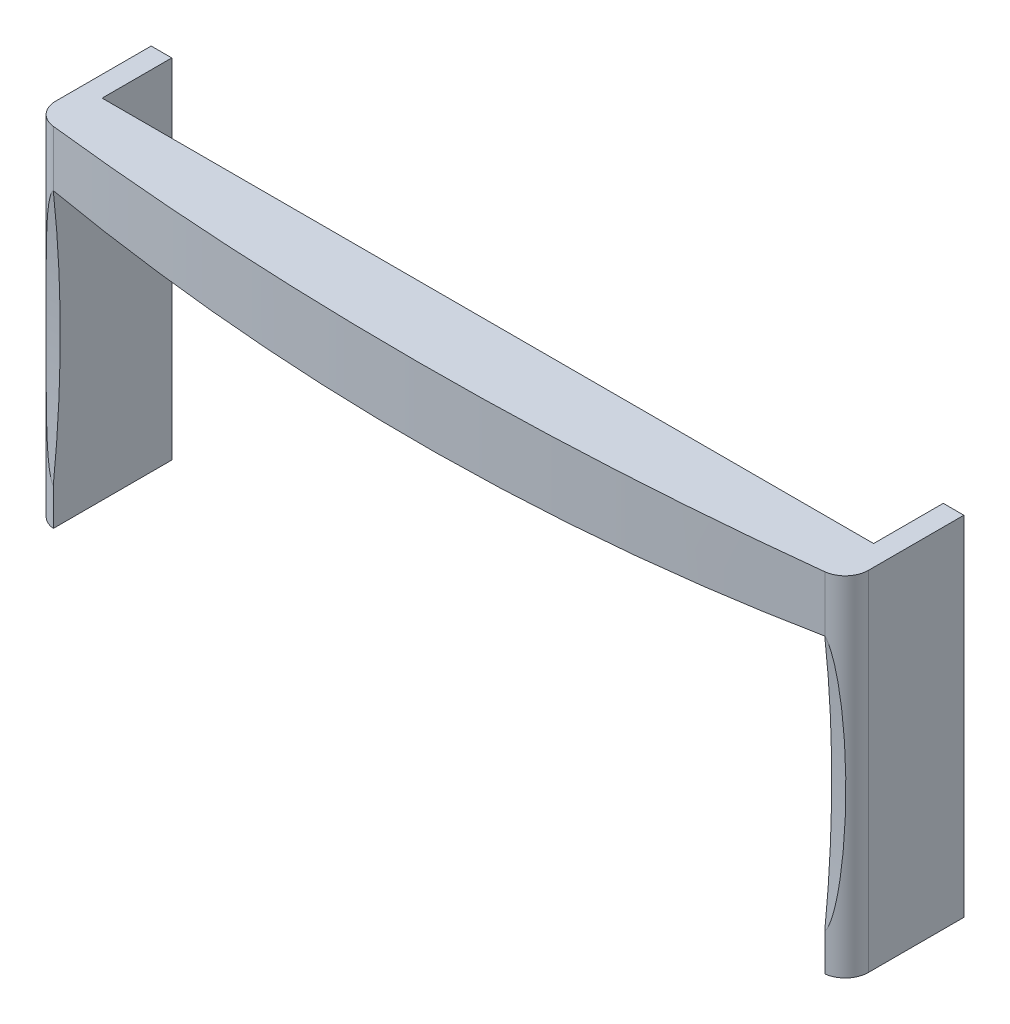
SolidWorks part; units mm, degrees
ref_plane "Front Plane" through (0, 0, 0) normal (0, 0, 1) x (1, 0, 0)
ref_plane "Top Plane" through (0, 0, 0) normal (0, 1, 0) x (1, 0, 0)
ref_plane "Right Plane" through (0, 0, 0) normal (1, 0, 0) x (0, 0, -1)
sketch "Sketch1" plane through (0, 0, 0) normal (0, 1, 0) x (1, 0, 0)
  line L0 (-87.5, 2.5) -> (-87.5, 12.5)
  line L5 (-87.5, 2.5) -> (87.5, -2.5) construction
  line L6 (-87.5, -2.5) -> (87.5, 2.5) construction
  line L7 (-87.5, 12.5) -> (87.5, 12.5)
  line L8 (87.5, 12.5) -> (87.5, 2.5)
  line L9 (-87.5, 2.5) -> (87.5, 2.5) construction
  arc A0 (-87.5, 2.5) -> (87.5, 2.5) centre (0, 735.8592) ccw
  point P0 (0, 0)
  point P9 (0, 2.5)
  point P10 (0, -2.7015)
  dimension "D1" = 175
  dimension "D2" = 5
  dimension "D3" = 10
  dimension "D4" = 5.2015
extrude "Boss-Extrude1" add sketch "Sketch1" along normal blind 75
fillet "Fillet1" radius 5 2 edges at (87.5, 37.5, -2.5) (-87.5, 37.5, -2.5)
sketch "Sketch2" plane through (0, 0, 0) normal (0, 0, 1) x (1, 0, 0)
  line L0 (-83.0623, 75) -> (-83.0623, 0) construction
  line L2 (-83.0623, 63) -> (-83.0623, 0)
  line L3 (-83.0623, 0) -> (83.0623, 0)
  line L4 (83.0623, 63) -> (83.0623, 0)
  line L6 (-87.5, 0) -> (-87.5, 75) construction
  line L7 (87.5, 75) -> (87.5, 0) construction
  line L8 (-83.0623, 63) -> (83.0623, 63) construction
  arc A0 (-83.0623, 63) -> (83.0623, 63) centre (0, 1211.3917) ccw
  point P8 (0, 63)
  point P13 (0, 60)
  dimension "D1" = 3
  dimension "D2" = 4.4377
  dimension "D3" = 4.4377
  dimension "D4" = 166.1247
extrude "Cut-Extrude1" cut sketch "Sketch2" against normal through all both and the other way through all
sketch "Sketch3" plane through (-87.5, 0, 0) normal (-1, 0, 0) x (0, 0, 1)
  line L2 (-1.9841, 63) -> (-1.9841, 8)
  line L3 (-1.9841, 63) -> (-1.9841, 0) construction
  arc A1 (-1.9841, 8) -> (-1.9841, 63) centre (249.3492, 35.5) cw
  point P5 (-3.4841, 35.5)
  point P7 (-1.9841, 35.5)
  dimension "D1" = 1.5
  dimension "D2" = 8
extrude "Cut-Extrude2" cut sketch "Sketch3" against normal through all both
sketch "Sketch4" plane through (0, 0, -12.5) normal (0, 0, -1) x (-1, 0, 0)
  line L1 (-87.5, 75) -> (-83.0623, 75)
  line L2 (-87.5, 75) -> (-87.5, 0)
  line L3 (-87.5, 0) -> (-83.0623, 0)
  line L4 (-83.0623, 75) -> (-83.0623, 0)
  line L5 (87.5, 75) -> (83.0623, 75)
  line L6 (87.5, 75) -> (87.5, 0)
  line L7 (87.5, 0) -> (83.0623, 0)
  line L8 (83.0623, 75) -> (83.0623, 0)
extrude "Boss-Extrude2" add sketch "Sketch4" along normal blind 15
